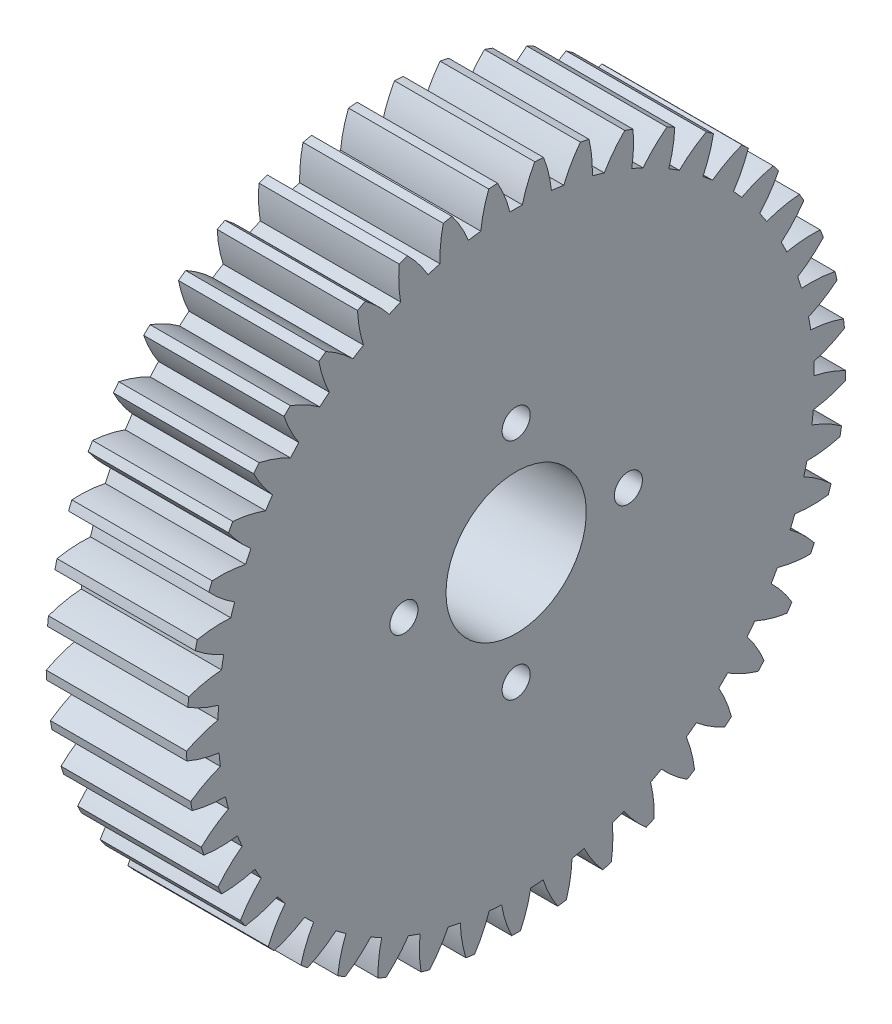
SolidWorks part; units mm, degrees
ref_plane "Plane1" through (0, 0, 0) normal (0, 0, 1) x (1, 0, 0)
ref_plane "Plane2" through (0, 0, 0) normal (0, 1, 0) x (1, 0, 0)
ref_plane "Plane3" through (0, 0, 0) normal (1, 0, 0) x (0, 0, -1)
sketch "HoldingSke" plane through (0, 0, 0) normal (0, 1, 0) x (1, 0, 0)
  line L0 (0, 0) -> (0.7071, -0.7071)
  line L1 (-15, 0) -> (100, 0) construction
  line L2 (0, 0) -> (-2.1039, 2.3779)
  line L3 (0, 0) -> (-11.863, 4.5341)
  line L4 (0, 0) -> (6.1066, 6.1066)
  line L5 (0, 0) -> (-46.8476, -17.4728)
  line L6 (0, 0) -> (-8.2896, -5.593)
  line L7 (-2.1039, 2.3779) -> (8.6586, 51.2059)
  line L8 (-76.2, 54.61) -> (-74.4, 54.61)
  line L9 (-71.009, 38.7566) -> (-53.1078, 45.2721)
  line L10 (-76.2, 71.12) -> (104.1128, 71.12)
  line L11 (0, 0) -> (-10, 0)
  line L12 (-76.2, 101.6) -> (-76.162, 101.6)
  line L13 (24.9733, 27.94) -> (52.9518, 28.4284)
  line L14 (24.9733, 27.94) -> (24.9743, 27.94)
  line L15 (24.9733, 27.94) -> (100.4006, 29.5858)
  line L16 (-63.627, -1) -> (-12.827, -1)
  circle A0 centre (0, 0) radius 5
  circle A1 centre (0, 0) radius 21.249
  circle A2 centre (0, 0) radius 37.5
  circle A3 centre (0, 0) radius 5
  dimension "MHD" = 42.498
  dimension "Hub_dia" = 75
  dimension "Bore" = 10
  dimension "MBD" = 10
  dimension "Num_teeth" = 45
  dimension "Pitch" = 1
  dimension "Overall_len" = 50
  dimension "Show_teeth" = 45
  dimension "Thickness" = 10
  dimension "OAL" = 50.0001
  dimension "T_dim" = 1.8
  dimension "Ap" = 20
  dimension "H" = 19.05
  dimension "Pitch_radius" = 180.3128
  dimension "Width" = 10
  dimension "Backlash" = 0.038
  dimension "Addendum_fac" = 1
  dimension "Dedendum_fac" = 1.25
  dimension "Clearance_fac" = 0.25
  dimension "Dedendum_add" = 0.001
  dimension "Module" = 1
sketch "BasProSke" plane through (0, 0, 0) normal (0, 1, 0) x (1, 0, 0)
  line L0 (-10, 0) -> (60, 0) construction
  line L1 (0, 0) -> (0, 23.5)
  line L2 (0, 0) -> (10, 0)
  line L3 (10, 0) -> (10, 23.5)
  line L4 (10, 23.5) -> (0, 23.5)
  dimension "Thickness" = 10
  dimension "Diameter" = 47
revolve "Base-Revolve" add sketch "BasProSke" angle 360 about L0
sketch "TooCutSke" plane through (0, 0, 0) normal (1, 0, 0) x (0, 0, -1)
  line L1 (0, 0) -> (0, 107) construction
  line L2 (0, 0) -> (-0.8517, 22.4839) construction
  line L3 (0, 0) -> (-3.1374, 44.8675) construction
  line L4 (-0.8517, 22.4839) -> (-1.5687, 22.4337) construction
  arc A0 (0.4426, 21.2444) -> (-0.4426, 21.2444) centre (0, 0) ccw
  arc A1 (1.3407, 23.4872) -> (-1.3407, 23.4872) centre (0, 0) ccw
  circle A2 centre (0, 0) radius 22.5 construction
  circle A3 centre (0, 0) radius 21.1431 construction
  arc A4 (-0.4426, 21.2444) -> (-1.3407, 23.4872) centre (-9.1711, 19.0505) ccw
  arc A5 (1.3407, 23.4872) -> (0.4426, 21.2444) centre (9.1711, 19.0505) ccw
  dimension "Root_dia" = 42.498
  dimension "Overcut_dia" = 47.0508
  dimension "Pitch_dia" = 45
  dimension "Base_dia" = 42.2862
  dimension "Flank_rad" = 9
  dimension "Half_ang" = 4
  dimension "Half_CT" = 0.7187
extrude "ToothCut" cut sketch "TooCutSke" along normal through all
fillet "Breaks" [suppressed] radius 0.02
fillet "RootFillets" [suppressed] radius 0.251
pattern_circular "TeethCuts" count 45 every 8 about axis through (-10, 0, 0) along (1, 0, 0) of "ToothCut", "RootFillets", "Breaks"
sketch "HubNeaOneSke" plane through (0, 0, 0) normal (-1, 0, 0) x (0, 0, 1)
  circle A0 centre (0, 0) radius 21.249
  dimension "Diameter" = 42.498
extrude "HubNearOne" [suppressed] add sketch "HubNeaOneSke" along normal blind 40.0001
sketch "HubNeaBotSke" plane through (0, 0, 0) normal (-1, 0, 0) x (0, 0, 1)
  circle A0 centre (0, 0) radius 21.249
  dimension "Diameter" = 42.498
extrude "HubNearBoth" [suppressed] add sketch "HubNeaBotSke" along normal blind 20
ref_plane "FarPln" through (10, 0, 0) normal (1, 0, 0) x (0, 0, -1)
sketch "HubFarSke" plane through (10, 0, 0) normal (1, 0, 0) x (0, 0, -1)
  circle A0 centre (0, 0) radius 21.249
  dimension "Diameter" = 42.498
extrude "HubFar" [suppressed] add sketch "HubFarSke" along normal blind 20
sketch "BorSke" plane through (0, 0, 0) normal (1, 0, 0) x (0, 0, -1)
  circle A0 centre (0, 0) radius 5
  dimension "Diameter" = 10
extrude "Bore" cut sketch "BorSke" along normal mid plane 100.0001
sketch "KeySke" plane through (0, 0, 0) normal (1, 0, 0) x (0, 0, -1)
  line L0 (-2, 0) -> (-2, 6.8)
  line L1 (-2, 6.8) -> (2, 6.8)
  line L2 (2, 6.8) -> (2, 0)
  line L3 (0, 0) -> (0, 34) construction
  line L4 (-2, 0) -> (2, 0)
  dimension "Offset" = 6.8
  dimension "Width" = 4
extrude "Keyway" [suppressed] cut sketch "KeySke" along normal mid plane 100.0001
pattern_circular "Keyway2" [suppressed] count 2 every 90 about axis through (-10, 0, 0) along (1, 0, 0)
hole_wizard "Dégagement M21" positions "Esquisse1" profile "Esquisse2" hole size "M2" standard "ISO" end condition up to next
sketch "Esquisse1" plane through (10, 0, 0) normal (1, 0, 0) x (0, 0, -1)
  point P0 (0, 8)
  point P6 (8, 0)
  point P7 (0, -8)
  point P8 (-8, 0)
  point P9 (0, 0)
  dimension "D1" = 4
sketch "Esquisse2" plane through (10, 8, 0) normal (0, 1, 0) x (0, 0, -1)
  line L0 (0, 0) -> (0, 10)
  line L1 (0, 10) -> (1, 10)
  line L2 (1, 10) -> (1, 0)
  line L5 (1, 0) -> (0, 0)
  line L11 (0, -6.35) -> (0, 107.95) construction
  dimension "Diamètre du perçage jusqu'au prochain" = 2
  dimension "Profondeur du perçage jusqu'au prochain" = 10
equation "' \"Module@HoldingSke\" = 6.35"
equation "' \"Num_teeth@HoldingSke\" = 12"
equation "' \"Ap@HoldingSke\" =  20"
equation "' \"Ap@HoldingSke\" = 20"
equation "' \"Width@HoldingSke\" = 0.5 * 25.4"
equation "' \"Hub_dia@HoldingSke\"= 1 * 25.4"
equation "' \"Hub_dia@HoldingSke\" = 1 * 25.4"
equation "' \"Overall_len@HoldingSke\" = 1.0 * 25.4"
equation "' \"Bore@HoldingSke\" = 0.75 * 25.4"
equation "' \"T_dim@HoldingSke\" = 0.1 * 25.4"
equation "' \"Width@KeySke\" = 0.25 * 25.4"
equation "' \"Show_teeth@HoldingSke\" = 13"
equation "' \"Backlash@HoldingSke\" = 0.009 * 25.4"
equation "' \"Addendum_fac@HoldingSke\" = 1.0"
equation "' \"Dedendum_fac@HoldingSke\" = 1.25"
equation "' \"Dedendum_add@HoldingSke\" = 0.00005 * 25.4"
equation "' \"Clearance_fac@HoldingSke\" = 0.25"
equation "\"Pitch@HoldingSke\" = 1 / \"Module@HoldingSke\""
equation "\"Overcut_dia@TooCutSke\" = (\"Num_teeth@HoldingSke\" + 2 * \"Addendum_fac@HoldingSke\") / \"Pitch@HoldingSke\" + 0.002 * 25.4"
equation "\"Pitch_dia@TooCutSke\" = \"Num_teeth@HoldingSke\" / \"Pitch@HoldingSke\""
equation "\"Base_dia@TooCutSke\" = \"Num_teeth@HoldingSke\" / \"Pitch@HoldingSke\" * cos((\"Ap@HoldingSke\"  * 3.14159265 / 180))"
equation "\"Root_dia@TooCutSke\" = (\"Num_teeth@HoldingSke\" + 2) / \"Pitch@HoldingSke\" - 2 * (\"Addendum_fac@HoldingSke\" + \"Dedendum_fac@HoldingSke\") / \"Pitch@HoldingSke\" - \"Dedendum_add@HoldingSke\" * 2"
equation "\"Half_ang@TooCutSke\" = 180 / \"Num_teeth@HoldingSke\""
equation "\"Half_CT@TooCutSke\" = \"Num_teeth@HoldingSke\" / \"Pitch@HoldingSke\" * sin((3.14159265 / 2 / \"Num_teeth@HoldingSke\")) / 2 - 7 * \"Backlash@HoldingSke\" / 4"
equation "\"Flank_rad@TooCutSke\" = \"Num_teeth@HoldingSke\" / \"Pitch@HoldingSke\" / 5"
equation "\"Radius@RootFillets\" = \"Clearance_fac@HoldingSke\" / \"Pitch@HoldingSke\" + \"Dedendum_add@HoldingSke\""
equation "\"Break_rad@Breaks\" = 0.02 / \"Pitch@HoldingSke\""
equation "\"Thickness@HoldingSke\" = \"Width@HoldingSke\""
equation "\"OAL@HoldingSke\" = \"Thickness@HoldingSke\""
equation "\"MHD@HoldingSke\" = (\"Num_teeth@HoldingSke\" + 2) / \"Pitch@HoldingSke\" - 2 * (\"Addendum_fac@HoldingSke\" + \"Dedendum_fac@HoldingSke\")  / \"Pitch@HoldingSke\" - \"Dedendum_add@HoldingSke\" * 2"
equation "\"MBD@HoldingSke\" = (\"Num_teeth@HoldingSke\" + 2) / \"Pitch@HoldingSke\" - 2 * (\"Addendum_fac@HoldingSke\" + \"Dedendum_fac@HoldingSke\")  / \"Pitch@HoldingSke\" - \"Dedendum_add@HoldingSke\" * 2 - 0.002 * 25.4"
equation "\"MHD@HoldingSke\" = ((sgn( \"MHD@HoldingSke\" - \"Hub_dia@HoldingSke\" )-1)*( \"MHD@HoldingSke\" - \"Hub_dia@HoldingSke\" ))/-2+ \"Hub_dia@HoldingSke\""
equation "\"MBD@HoldingSke\" = ((sgn( \"MBD@HoldingSke\" - \"Bore@HoldingSke\" )-1)*( \"MBD@HoldingSke\" - \"Bore@HoldingSke\" ))/-2+ \"Bore@HoldingSke\""
equation "\"OAL@HoldingSke\" = ((sgn( \"OAL@HoldingSke\" - \"Overall_len@HoldingSke\" )+1)*( \"OAL@HoldingSke\" - \"Overall_len@HoldingSke\" ))/2 + \"Overall_len@HoldingSke\" + 0.000002 * 25.4"
equation "\"Num_teeth@TeethCuts\" = int( \"Show_teeth@HoldingSke\" ) + 1"
equation "\"Num_teeth@TeethCuts\" = ((sgn( \"Num_teeth@TeethCuts\" - \"Num_teeth@HoldingSke\" )-1)*( \"Num_teeth@TeethCuts\" - \"Num_teeth@HoldingSke\" ))/-2+ \"Num_teeth@HoldingSke\""
equation "\"Num_teeth@TeethCuts\" = ((sgn( \"Num_teeth@TeethCuts\" - 2.0)+1)*( \"Num_teeth@TeethCuts\" - 2.0))/2 +2.0"
equation "\"Angle@TeethCuts\" = 360.0 / \"Num_teeth@HoldingSke\""
equation "\"Diameter@BasProSke\" = (\"Num_teeth@HoldingSke\" + 2 * \"Addendum_fac@HoldingSke\") / \"Pitch@HoldingSke\""
equation "\"Thickness@BasProSke\"  = \"Thickness@HoldingSke\""
equation "' \"Fillet_rad@BasProSke\" =  \"Thickness@HoldingSke\" * 0.05"
equation "' \"Fillet_rad@BasProSke\" = \"Thickness@HoldingSke\" * 0.05"
equation "\"MHD@HoldingSke\" = ((sgn( \"MHD@HoldingSke\" - \"Root_dia@TooCutSke\" )-1)*( \"MHD@HoldingSke\" - \"Root_dia@TooCutSke\" ))/-2+ \"Root_dia@TooCutSke\""
equation "\"Diameter@HubNeaOneSke\" = \"MHD@HoldingSke\""
equation "\"Length@HubNearOne\" = \"OAL@HoldingSke\" - \"Thickness@BasProSke\""
equation "\"Diameter@HubNeaBotSke\" = \"MHD@HoldingSke\""
equation "\"Length@HubNearBoth\" = ( \"OAL@HoldingSke\" - \"Thickness@BasProSke\" ) / 2.0"
equation "\"Thickness@FarPln\" = \"Thickness@BasProSke\""
equation "\"Diameter@HubFarSke\" = \"MHD@HoldingSke\""
equation "\"Length@HubFar\" = ( \"OAL@HoldingSke\" - \"Thickness@BasProSke\" ) / 2.0"
equation "\"Diameter@BorSke\" = \"MBD@HoldingSke\""
equation "\"D1@Bore\" = \"OAL@HoldingSke\" * 2.0"
equation "\"D1@Keyway\" = \"OAL@HoldingSke\" * 2.0"
equation "\"Offset@KeySke\" = \"T_dim@HoldingSke\" + \"MBD@HoldingSke\" / 2.0"
